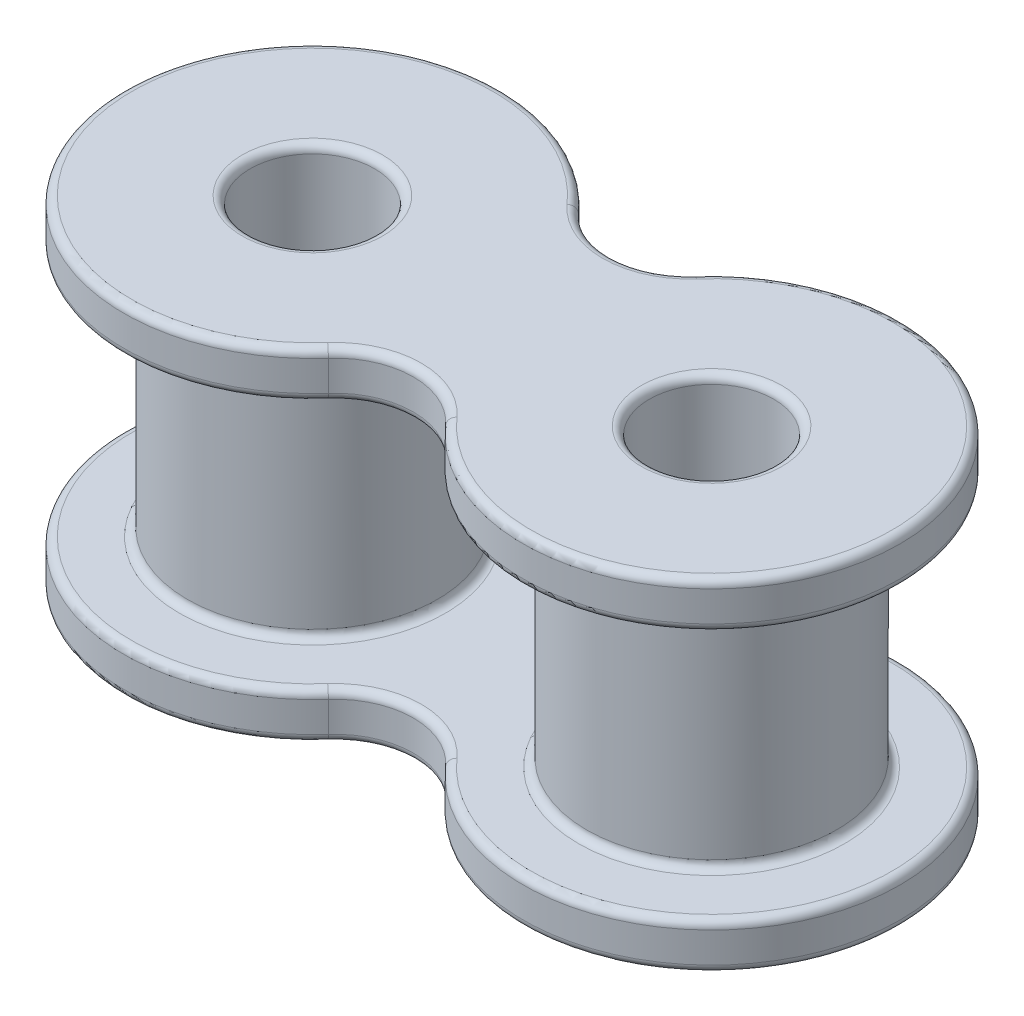
SolidWorks part; units mm, degrees
material "Alloy Steel"
ref_plane "X-Y Datum" through (0, 0, 0) normal (0, 0, 1) x (1, 0, 0)
ref_plane "X-Z Datum" through (0, 0, 0) normal (0, 1, 0) x (1, 0, 0)
ref_plane "Y-Z Datum" through (0, 0, 0) normal (1, 0, 0) x (0, 0, -1)
sketch "Sketch1" plane through (0, 0, 0) normal (0, 1, 0) x (1, 0, 0)
  line L0 (0, 9.8489) -> (0, -11.4215) construction
  line L1 (-12.6403, 0) -> (12.9549, 0) construction
  circle A0 centre (-6.35, 0) radius 1.9812
  arc A1 (-1.8654, 3.9776) -> (-1.8654, -3.9776) centre (-6.35, 0) ccw
  arc A2 (1.8654, 3.9776) -> (1.8654, -3.9776) centre (6.35, 0) cw
  circle A3 centre (6.35, 0) radius 1.9812
  arc A4 (-1.8654, 3.9776) -> (1.8654, 3.9776) centre (0, 5.6322) ccw
  arc A5 (-1.8654, -3.9776) -> (1.8654, -3.9776) centre (0, -5.6322) cw
  dimension "D1" = 11.9888
  dimension "D2" = 3.9624
  dimension "D4" = 2.4935
  dimension "D3" = 6.35
extrude "Boss-Extrude1" add sketch "Sketch1" along normal mid plane 1.4732
sketch "Sketch5" plane through (0, 0.7366, 0) normal (0, 1, 0) x (1, 0, 0)
  line L0 (0, -55) -> (0, 55) construction
  circle A0 centre (6.35, 0) radius 1.9812 construction
  circle A1 centre (6.35, 0) radius 1.9812
  circle A2 centre (-6.35, 0) radius 1.9812
  circle A3 centre (6.35, 0) radius 3.9751
  circle A4 centre (-6.35, 0) radius 3.9751
  dimension "D1" = 7.9502
extrude "Boss-Extrude2" add sketch "Sketch5" along normal blind 7.9248
fillet "Fillet" radius 0.254 12 edges at (0, 0.7366, -3.1387) (12.3444, 0.7366, 0) (0, 0.7366, 3.1387) (-12.3444, -0.7366, 0) (0, -0.7366, -3.1387) (-12.3444, 0.7366, 0) (6.35, -0.7366, -1.9812) (-6.35, -0.7366, 1.9812) (0, -0.7366, 3.1387) (12.3444, -0.7366, 0) (6.35, 0.7366, 3.9751) (-6.35, 0.7366, -3.9751)
ref_plane "Center Plane" through (0, 4.699, 0) normal (0, 1, 0) x (1, 0, 0)
mirror "Mirror2" about plane through (0, 4.699, 0) normal (0, 1, 0) of "Fillet", "Boss-Extrude1"
ref_plane "Plane1" through (0, 4.699, 0) normal (0, 1, 0) x (1, 0, 0)
